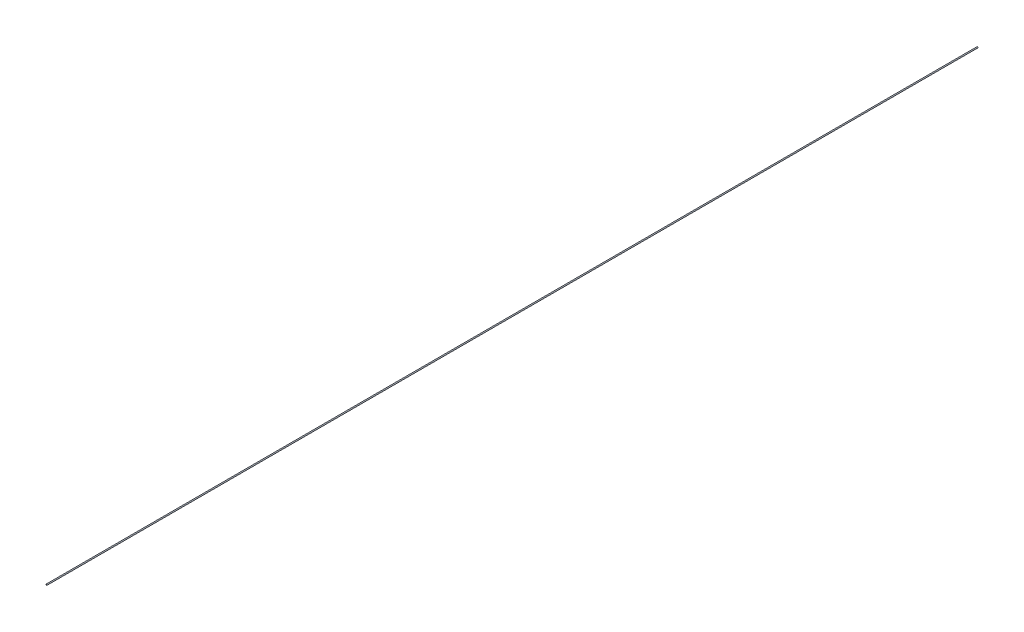
SolidWorks part; units mm, degrees
ref_plane "Front Plane" through (0, 0, 0) normal (0, 0, 1) x (1, 0, 0)
ref_plane "Top Plane" through (0, 0, 0) normal (0, 1, 0) x (1, 0, 0)
ref_plane "Right Plane" through (0, 0, 0) normal (1, 0, 0) x (0, 0, -1)
sketch "Sketch2" plane through (0, 0, 0) normal (0, 0, 1) x (1, 0, 0)
  circle A0 centre (0, 0) radius 6.35
  circle A1 centre (0, 0) radius 5.334
  dimension "D1" = 12.7
  dimension "D2" = 1.016
extrude "Boss-Extrude1" add sketch "Sketch2" along normal blind 11125.2
